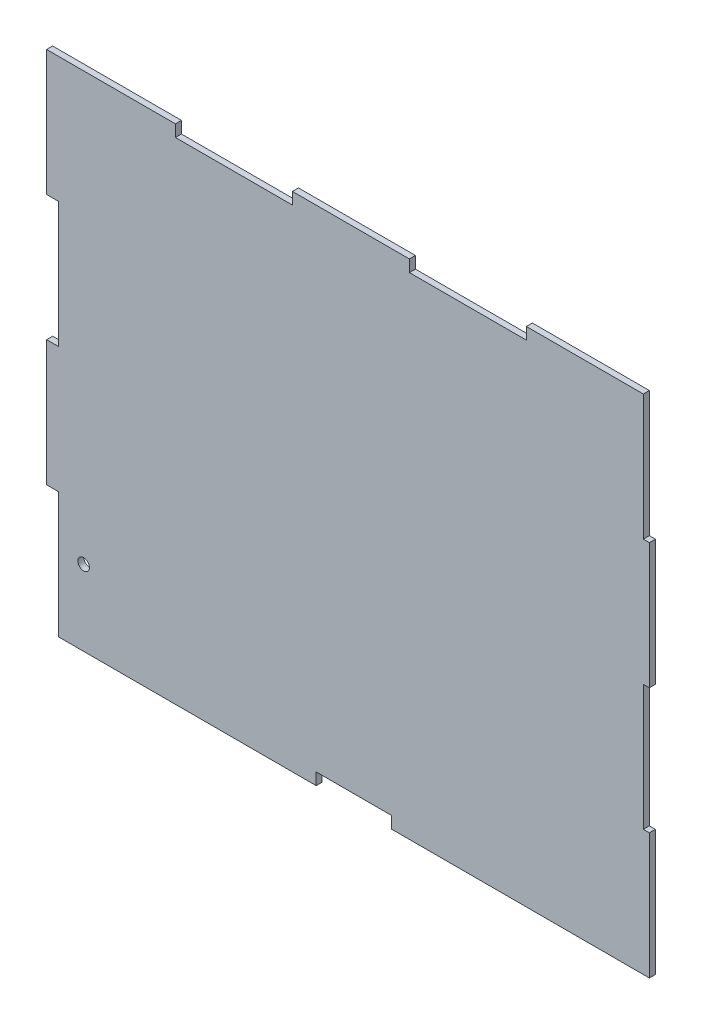
SolidWorks part; units mm, degrees
material "Acrylic (Medium-high impact)"
ref_plane "Front Plane" through (0, 0, 0) normal (0, 0, 1) x (1, 0, 0)
ref_plane "Top Plane" through (0, 0, 0) normal (0, 1, 0) x (1, 0, 0)
ref_plane "Right Plane" through (0, 0, 0) normal (1, 0, 0) x (0, 0, -1)
sketch "Sketch1" plane through (0, 0, 0) normal (0, 0, 1) x (1, 0, 0)
  line L0 (130.175, 0) -> (130.175, 5.9944)
  line L1 (0, 0) -> (130.175, 0)
  line L2 (-5.9944, 63.5) -> (-5.9944, 127)
  line L3 (-5.9944, 253.9293) -> (59.0804, 253.9293)
  line L4 (298.45, 0) -> (298.45, 63.5)
  line L5 (130.175, 5.9944) -> (168.275, 5.9944)
  line L6 (168.275, 5.9944) -> (168.275, 0)
  line L7 (0, 0) -> (0, 63.5)
  line L8 (0, 63.5) -> (-5.9944, 63.5)
  line L9 (0, 127) -> (-5.9944, 127)
  line L10 (0, 127) -> (0, 190.5)
  line L11 (0, 190.5) -> (-5.9944, 190.5)
  line L12 (-5.9944, 190.5) -> (-5.9944, 253.9293)
  line L13 (168.275, 0) -> (298.45, 0)
  line L14 (59.0804, 253.9293) -> (59.0804, 247.9603)
  line L15 (59.0804, 247.9603) -> (118.1608, 247.9603)
  line L16 (118.1608, 247.9603) -> (118.1608, 253.9293)
  line L17 (177.2412, 253.9293) -> (177.2412, 247.9603)
  line L18 (177.2412, 247.9603) -> (236.3216, 247.9603)
  line L19 (236.3216, 247.9603) -> (236.3216, 253.9293)
  line L20 (118.1608, 253.9293) -> (177.2412, 253.9293)
  line L21 (236.3216, 253.9293) -> (295.402, 253.9293)
  line L22 (298.45, 63.5) -> (295.402, 63.5)
  line L23 (295.402, 63.5) -> (295.402, 126.9293)
  line L24 (295.402, 126.9293) -> (298.45, 126.9293)
  line L25 (298.45, 190.4293) -> (295.402, 190.4293)
  line L26 (295.402, 190.4293) -> (295.402, 253.9293)
  line L29 (298.45, 126.9293) -> (298.45, 190.4293)
  dimension "D1" = 254
  dimension "D2" = 298.45
  dimension "D3" = 5.9944
  dimension "D4" = 38.1
  dimension "D5" = 130.175
  dimension "D6" = 63.5
  dimension "D7" = 5.9944
  dimension "D8" = 5.969
  dimension "D9" = 59.0804
  dimension "D10" = 3.048
extrude "Boss-Extrude1" add sketch "Sketch1" along normal blind 3.048
sketch "Sketch2" plane through (0, 0, 3.048) normal (0, 0, 1) x (1, 0, 0)
  line L0 (0, 0) -> (130.175, 0) construction
  line L1 (0, 63.5) -> (0, 0) construction
  circle A0 centre (12.7, 38.1) radius 2.921
  dimension "D1" = 5.842
  dimension "D2" = 38.1
  dimension "D3" = 12.7
extrude "Cut-Extrude1" cut sketch "Sketch2" against normal up to next
